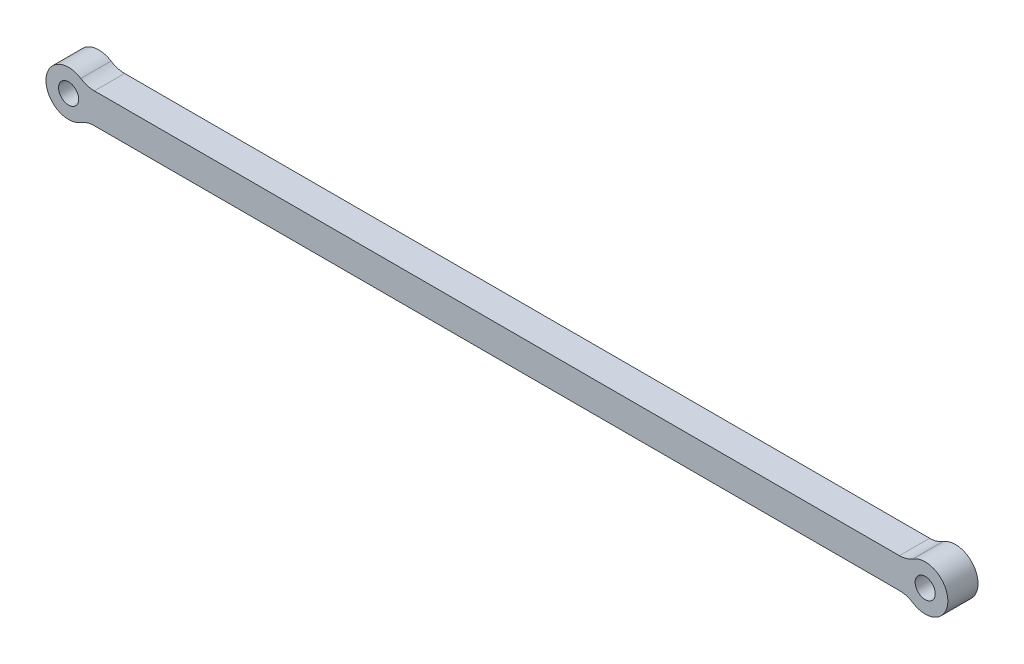
SolidWorks part; units mm, degrees
material "Brass"
ref_plane "Front" through (0, 0, 0) normal (0, 0, 1) x (1, 0, 0)
ref_plane "Top" through (0, 0, 0) normal (0, 1, 0) x (1, 0, 0)
ref_plane "Right" through (0, 0, 0) normal (1, 0, 0) x (0, 0, -1)
sketch "Sketch1" plane through (0, 0, 0) normal (0, 0, 1) x (1, 0, 0)
  line L0 (0, 0) -> (340.4001, 0) construction
  line L1 (6.7082, 6) -> (333.6919, 6)
  line L2 (6.7082, -6) -> (333.6919, -6)
  circle A0 centre (0, 0) radius 4
  circle A1 centre (340.4001, 0) radius 4
  arc A4 (6.7082, 6) -> (6.7082, -6) centre (0, 0) ccw
  arc A5 (333.6919, -6) -> (333.6919, 6) centre (340.4001, 0) ccw
  point P4 (170.2, 0)
  dimension "D2" = 8
  dimension "D4" = 18
  dimension "D1" = 340.4001
  dimension "D3" = 12
  dimension "D5" = 6
extrude "Boss-Extrude1" add sketch "Sketch1" along normal blind 12 contours L1 L2
fillet "Fillet1" radius 10 4 edges at (333.6919, 6, 6) (333.6919, -6, 6) (6.7082, -6, 6) (6.7082, 6, 6)
